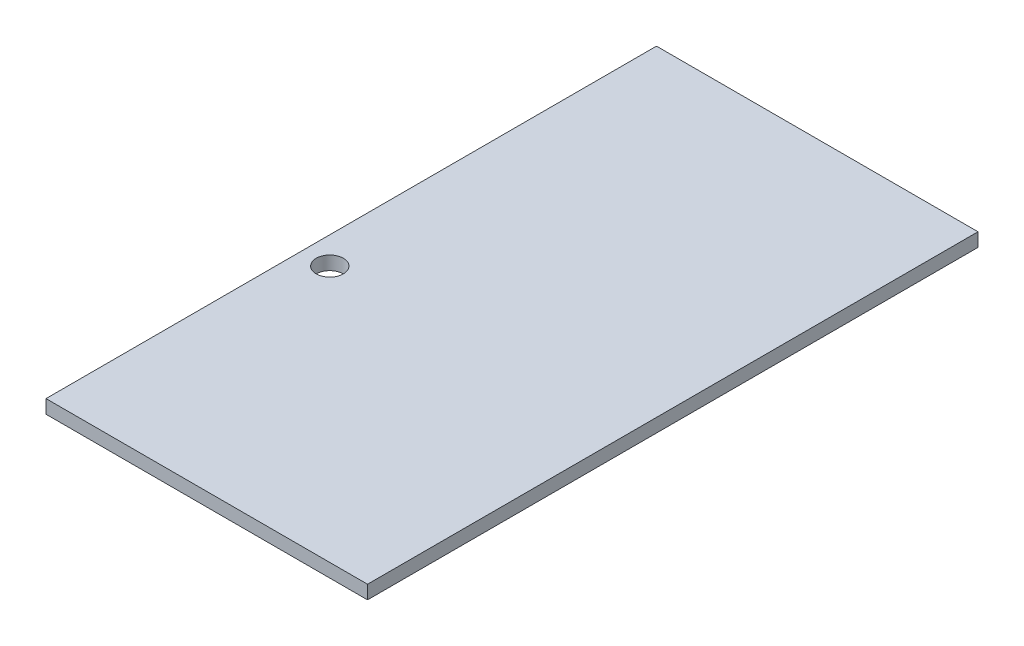
SolidWorks part; units mm, degrees
ref_plane "Front Plane" through (0, 0, 0) normal (0, 0, 1) x (1, 0, 0)
ref_plane "Top Plane" through (0, 0, 0) normal (0, 1, 0) x (1, 0, 0)
ref_plane "Right Plane" through (0, 0, 0) normal (1, 0, 0) x (0, 0, -1)
sketch "Croquis1" plane through (0, 0, 0) normal (0, 1, 0) x (1, 0, 0)
  line L1 (-118.5, -225) -> (118.5, -225)
  line L2 (-118.5, -225) -> (-118.5, 225)
  line L3 (-118.5, 225) -> (118.5, 225)
  line L4 (118.5, -225) -> (118.5, 225)
  point P4 (0, 225)
  point P6 (-118.5, 0)
  dimension "D1" = 450
  dimension "D2" = 237
extrude "Saliente-Extruir1" add sketch "Croquis1" along normal blind 10
sketch "Croquis2" plane through (0, 0, 0) normal (0, -1, 0) x (1, 0, 0)
  line L0 (-118.5, 225) -> (-113.5, 225)
  line L1 (-118.5, 225) -> (118.5, 225) construction
  line L2 (-113.5, 225) -> (-113.5, -225)
  line L3 (118.5, -225) -> (-118.5, -225) construction
  line L4 (-113.5, -225) -> (-118.5, -225)
  line L5 (-118.5, -225) -> (-118.5, 225)
  dimension "D1" = 5
extrude "Saliente-Extruir2" add sketch "Croquis2" along normal blind 70
sketch "Croquis3" plane through (-113.5, 0, 0) normal (1, 0, 0) x (0, 0, -1)
  line L0 (225, 0) -> (-225, 0) construction
  line L1 (-225, -70) -> (-225, 0) construction
  line L2 (225, -70) -> (225, 0) construction
  line L3 (-225, -35) -> (225, -35) construction
  circle A0 centre (-215, -10) radius 2
  circle A1 centre (215, -10) radius 2
  circle A2 centre (215, -60) radius 2
  circle A3 centre (-215, -60) radius 2
  dimension "D5" = 4
  dimension "D6" = 4
  dimension "D1" = 10
  dimension "D2" = 10
  dimension "D3" = 10
  dimension "D4" = 10
extrude "Cortar-Extruir1" cut sketch "Croquis3" against normal blind 70
sketch "Croquis4" plane through (-113.5, 0, 0) normal (1, 0, 0) x (0, 0, -1)
  line L0 (-225, -70) -> (-225, 0)
  line L1 (-225, 0) -> (225, 0)
  line L2 (225, 0) -> (225, -70)
  line L3 (225, -70) -> (-225, -70)
extrude "Cortar-Extruir2" cut sketch "Croquis4" against normal blind 10
sketch "Croquis5" plane through (0, 0, 0) normal (0, -1, 0) x (1, 0, 0)
  line L0 (-118.5, 20.8) -> (-77.5, 20.8)
  line L1 (-118.5, -225) -> (-118.5, 225) construction
  line L2 (-77.5, 20.8) -> (-77.5, 50.8)
  line L3 (-77.5, 50.8) -> (-118.5, 50.8)
  circle A1 centre (-98.5, 35.8) radius 10
  dimension "D4" = 20
  dimension "D1" = 174.2
  dimension "D2" = 30
  dimension "D3" = 41
  dimension "D5" = 20
  dimension "D6" = 15
extrude "Cortar-Extruir4" cut sketch "Croquis5" against normal blind 10 contours A1
